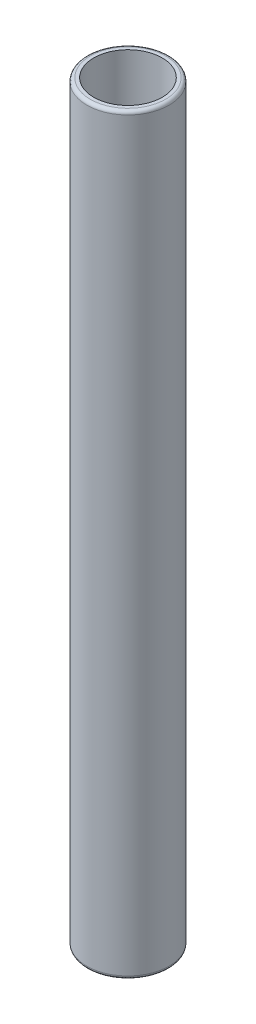
SolidWorks part; units mm, degrees
ref_plane "Front Plane" through (0, 0, 0) normal (0, 0, 1) x (1, 0, 0)
ref_plane "Top Plane" through (0, 0, 0) normal (0, 1, 0) x (1, 0, 0)
ref_plane "Right Plane" through (0, 0, 0) normal (1, 0, 0) x (0, 0, -1)
sketch "Sketch1" plane through (0, 0, 0) normal (0, 1, 0) x (1, 0, 0)
  circle A0 centre (0, 0) radius 6
  circle A1 centre (0, 0) radius 5
  dimension "D1" = 1
  dimension "D2" = 12
extrude "Boss-Extrude1" add sketch "Sketch1" along normal blind 110
fillet "Fillet1" radius 0.5 2 edges at (0, 110, 6) (0, 0, 6)
